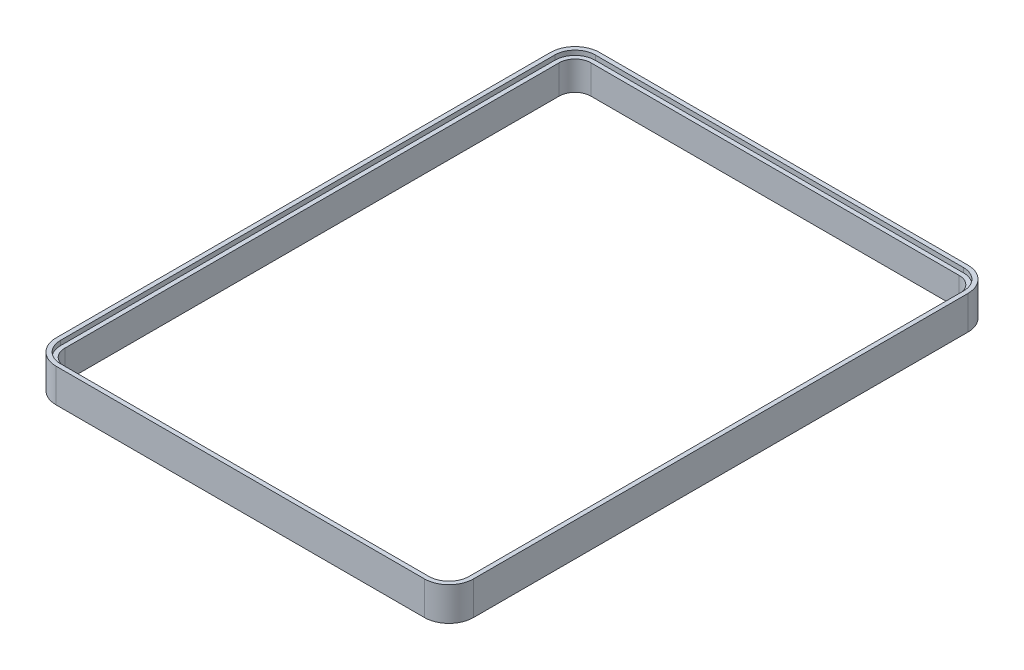
SolidWorks part; units mm, degrees
ref_plane "Front Plane" through (0, 0, 0) normal (0, 0, 1) x (1, 0, 0)
ref_plane "Top Plane" through (0, 0, 0) normal (0, 1, 0) x (1, 0, 0)
ref_plane "Right Plane" through (0, 0, 0) normal (1, 0, 0) x (0, 0, -1)
sketch "Sketch1" plane through (0, 0, 0) normal (0, 1, 0) x (1, 0, 0)
  line L0 (35.35, -42.75) -> (35.35, 42.75)
  line L1 (0, 0) -> (35.35, 0) construction
  line L2 (31.85, 46.25) -> (-31.85, 46.25)
  line L3 (0, 0) -> (0, 46.25) construction
  line L4 (-35.35, -42.75) -> (-35.35, 42.75)
  line L5 (31.85, -46.25) -> (-31.85, -46.25)
  line L6 (31.85, 47) -> (-31.85, 47)
  line L7 (-36.1, -42.75) -> (-36.1, 42.75)
  line L8 (31.85, -47) -> (-31.85, -47)
  line L9 (36.1, -42.75) -> (36.1, 42.75)
  arc A0 (35.35, 42.75) -> (31.85, 46.25) centre (31.85, 42.75) ccw
  arc A2 (-35.35, 42.75) -> (-31.85, 46.25) centre (-31.85, 42.75) cw
  arc A3 (35.35, -42.75) -> (31.85, -46.25) centre (31.85, -42.75) cw
  arc A4 (-35.35, -42.75) -> (-31.85, -46.25) centre (-31.85, -42.75) ccw
  arc A5 (-36.1, 42.75) -> (-31.85, 47) centre (-31.85, 42.75) cw
  arc A6 (-36.1, -42.75) -> (-31.85, -47) centre (-31.85, -42.75) ccw
  arc A7 (36.1, -42.75) -> (31.85, -47) centre (31.85, -42.75) cw
  arc A8 (36.1, 42.75) -> (31.85, 47) centre (31.85, 42.75) ccw
  point P3 (35.35, 0)
  point P18 (-35.35, 0)
  dimension "D3" = 3.5
  dimension "D4" = 0.75
  dimension "D1" = 42.75
  dimension "D2" = 35.35
extrude "Boss-Extrude1" add sketch "Sketch1" against normal blind 0.8
sketch "Sketch2" plane through (0, -0.8, 0) normal (0, -1, 0) x (1, 0, 0)
  line L20 (-34.6, 42.75) -> (-34.6, -42.75)
  line L21 (-31.85, -45.5) -> (31.85, -45.5)
  line L22 (34.6, -42.75) -> (34.6, 42.75)
  line L23 (31.85, 45.5) -> (-31.85, 45.5)
  line L24 (36.1, -42.75) -> (36.1, 42.75)
  line L25 (-31.85, -47) -> (31.85, -47)
  line L26 (-36.1, 42.75) -> (-36.1, -42.75)
  line L27 (31.85, 47) -> (-31.85, 47)
  line L28 (36.1, -42.75) -> (36.1, 42.75)
  line L29 (-31.85, -47) -> (31.85, -47)
  line L30 (-36.1, 42.75) -> (-36.1, -42.75)
  line L31 (31.85, 47) -> (-31.85, 47)
  arc A16 (-31.85, 45.5) -> (-34.6, 42.75) centre (-31.85, 42.75) ccw
  arc A17 (-34.6, -42.75) -> (-31.85, -45.5) centre (-31.85, -42.75) ccw
  arc A18 (31.85, -45.5) -> (34.6, -42.75) centre (31.85, -42.75) ccw
  arc A19 (34.6, 42.75) -> (31.85, 45.5) centre (31.85, 42.75) ccw
  arc A20 (36.1, 42.75) -> (31.85, 47) centre (31.85, 42.75) ccw
  arc A21 (31.85, -47) -> (36.1, -42.75) centre (31.85, -42.75) ccw
  arc A22 (-36.1, -42.75) -> (-31.85, -47) centre (-31.85, -42.75) ccw
  arc A23 (-31.85, 47) -> (-36.1, 42.75) centre (-31.85, 42.75) ccw
  arc A24 (36.1, 42.75) -> (31.85, 47) centre (31.85, 42.75) ccw
  arc A25 (31.85, -47) -> (36.1, -42.75) centre (31.85, -42.75) ccw
  arc A26 (-36.1, -42.75) -> (-31.85, -47) centre (-31.85, -42.75) ccw
  arc A27 (-31.85, 47) -> (-36.1, 42.75) centre (-31.85, 42.75) ccw
  dimension "D1" = 0
  dimension "D2" = 1.5
extrude "Boss-Extrude2" add sketch "Sketch2" along normal blind 5
ref_plane "Plane1" through (0, -22.8, 0) normal (0, 1, 0) x (1, 0, 0)
sketch "Sketch4" plane through (0, -22.8, 0) normal (0, 1, 0) x (1, 0, 0)
  line L24 (24.6, -35.5) -> (24.6, 35.5)
  line L25 (-24.6, -35.5) -> (24.6, -35.5)
  line L26 (-24.6, 35.5) -> (-24.6, -35.5)
  line L27 (24.6, 35.5) -> (-24.6, 35.5)
  line L28 (24.6, -35.5) -> (24.6, 35.5)
  line L29 (-24.6, -35.5) -> (24.6, -35.5)
  line L30 (-24.6, 35.5) -> (-24.6, -35.5)
  line L31 (24.6, 35.5) -> (-24.6, 35.5)
  dimension "D1" = 10
